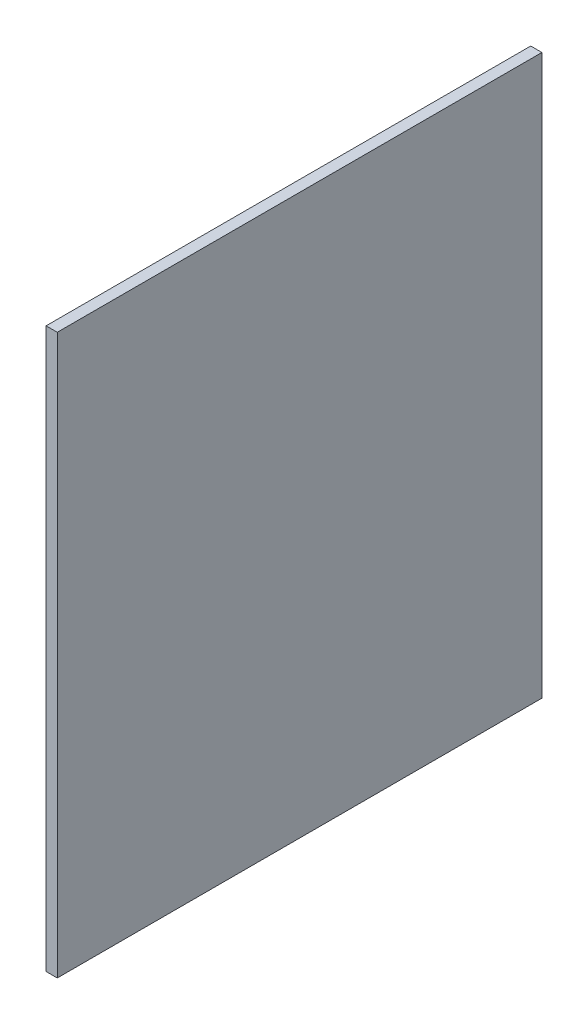
SolidWorks part; units mm, degrees
ref_plane "Front Plane" through (0, 0, 0) normal (0, 0, 1) x (1, 0, 0)
ref_plane "Top Plane" through (0, 0, 0) normal (0, 1, 0) x (1, 0, 0)
ref_plane "Right Plane" through (0, 0, 0) normal (1, 0, 0) x (0, 0, -1)
sketch "Sketch1" plane through (0, 0, 0) normal (1, 0, 0) x (0, 0, -1)
  line L1 (0, 0) -> (130, 0)
  line L2 (0, 0) -> (0, 150)
  line L3 (0, 150) -> (130, 150)
  line L4 (130, 0) -> (130, 150)
  dimension "D1" = 150
  dimension "D2" = 130
extrude "Boss-Extrude1" add sketch "Sketch1" along normal blind 3
